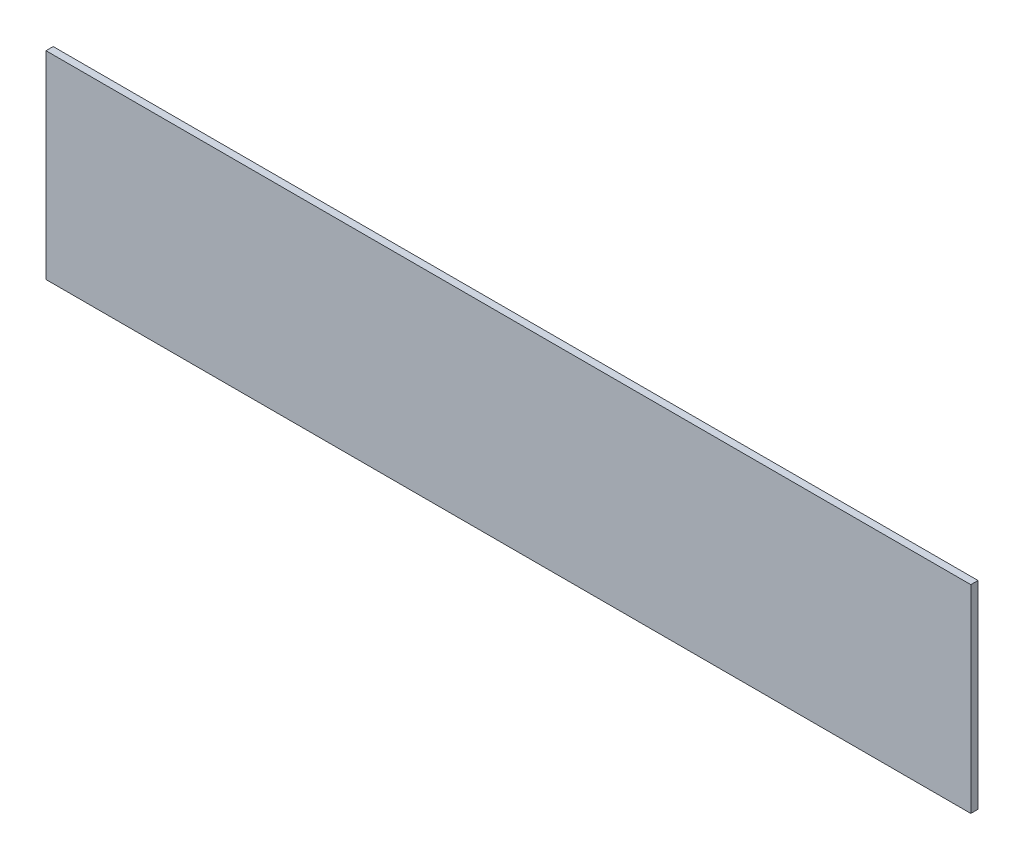
SolidWorks part; units mm, degrees
material "Acrílico (Impacto medio-alto)"
ref_plane "Alzado" through (0, 0, 0) normal (0, 0, 1) x (1, 0, 0)
ref_plane "Planta" through (0, 0, 0) normal (0, 1, 0) x (1, 0, 0)
ref_plane "Vista lateral" through (0, 0, 0) normal (1, 0, 0) x (0, 0, -1)
sketch "Croquis1" plane through (0, 0, 0) normal (0, 0, 1) x (1, 0, 0)
  line L1 (0, 0) -> (385, 0)
  line L2 (0, 0) -> (0, 82.5)
  line L3 (0, 82.5) -> (385, 82.5)
  line L4 (385, 0) -> (385, 82.5)
  dimension "D1" = 82.5
  dimension "D2" = 385
extrude "Saliente-Extruir1" add sketch "Croquis1" along normal blind 3
